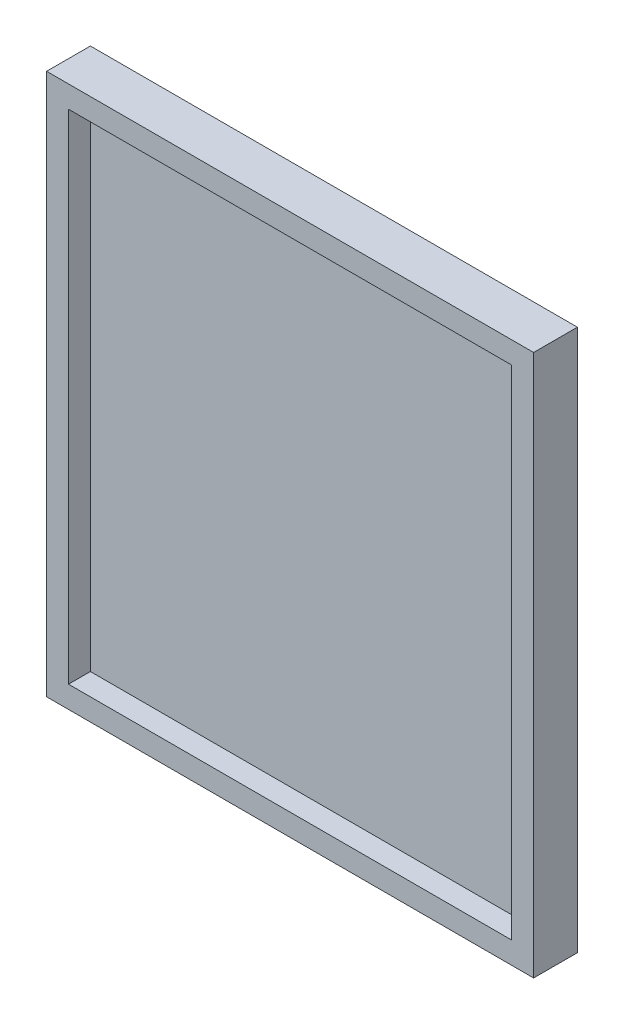
SolidWorks part; units mm, degrees
ref_plane "Front Plane" through (0, 0, 0) normal (0, 0, 1) x (1, 0, 0)
ref_plane "Top Plane" through (0, 0, 0) normal (0, 1, 0) x (1, 0, 0)
ref_plane "Right Plane" through (0, 0, 0) normal (1, 0, 0) x (0, 0, -1)
sketch "Sketch2" plane through (0, 0, 0) normal (0, 0, 1) x (1, 0, 0)
  line L1 (-70.6438, -78.5812) -> (70.6437, -78.5812)
  line L2 (-70.6438, -78.5812) -> (-70.6438, 78.5812)
  line L3 (-70.6438, 78.5812) -> (70.6437, 78.5812)
  line L4 (70.6437, -78.5812) -> (70.6437, 78.5812)
  line L5 (-70.6438, -78.5812) -> (70.6437, 78.5812) construction
  line L6 (-70.6438, 78.5812) -> (70.6437, -78.5812) construction
  point P0 (0, 0)
  dimension "D1" = 141.2875
  dimension "D2" = 157.1625
extrude "Boss-Extrude1" add sketch "Sketch2" along normal blind 12.7
shell "Shell1" thickness 6.35
equation "\"width\"= 5.5625in"
equation "\"height\"= 6.1875in"
equation "\"shell\"= 0.25in"
equation "\"D1@Sketch2\"=\"width\""
equation "\"D2@Sketch2\"=\"height\""
equation "\"extrude\"= 0.5in"
equation "\"D1@Boss-Extrude1\"=\"extrude\""
equation "\"D1@Shell1\"=\"shell\""
